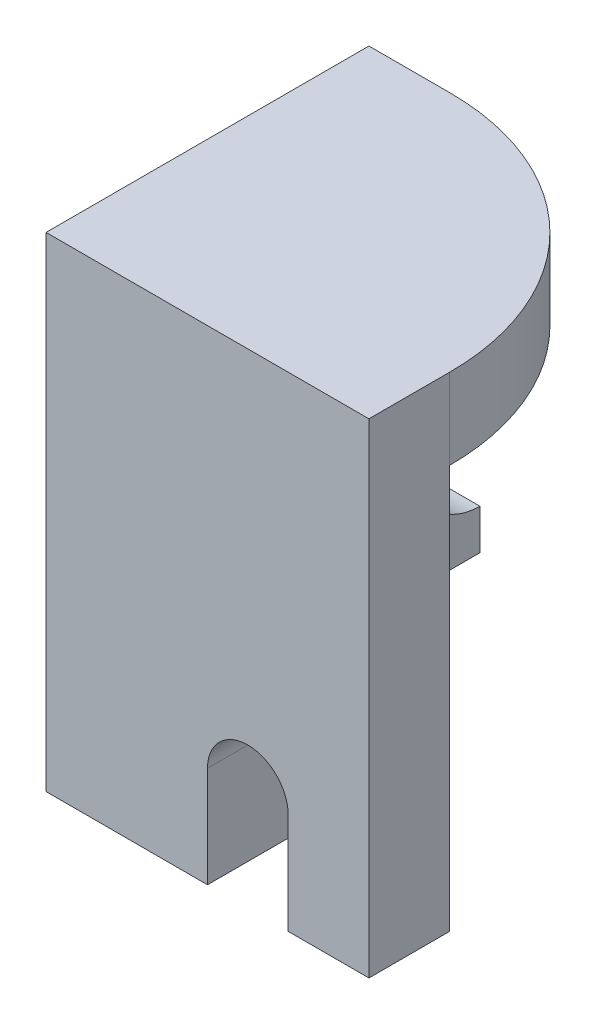
SolidWorks part; units mm, degrees
ref_plane "Front Plane" through (0, 0, 0) normal (0, 0, 1) x (1, 0, 0)
ref_plane "Top Plane" through (0, 0, 0) normal (0, 1, 0) x (1, 0, 0)
ref_plane "Right Plane" through (0, 0, 0) normal (1, 0, 0) x (0, 0, -1)
sketch "Sketch1" plane through (0, 0, 0) normal (0, 1, 0) x (1, 0, 0)
  line L0 (32, -32) -> (32, -16) construction
  line L1 (-32, 32) -> (-16, 32)
  line L2 (-32, 32) -> (-32, -32)
  line L3 (-32, -32) -> (32, -32)
  line L4 (32, -16) -> (32, -32)
  line L5 (-32, 32) -> (32, -32) construction
  line L6 (-32, -32) -> (32, 32) construction
  arc A0 (32, -16) -> (-16, 32) centre (-16, -16) ccw
  point P0 (0, 0)
  dimension "D3" = 48
  dimension "D1" = 64
  dimension "D2" = 64
extrude "Boss-Extrude1" add sketch "Sketch1" along normal blind 16
sketch "Sketch3" plane through (0, 0, 0) normal (0, -1, 0) x (1, 0, 0)
  line L0 (-32, -32) -> (-32, 32) construction
  line L1 (32, 32) -> (-32, 32)
  line L2 (32, 32) -> (32, 16)
  line L3 (32, 16) -> (-32, 16)
  line L4 (-32, 32) -> (-32, 16)
  dimension "D1" = 16
extrude "Boss-Extrude2" add sketch "Sketch3" along normal blind 80
sketch "Sketch4" plane through (0, 0, 16) normal (0, 0, -1) x (-1, 0, 0)
  line L0 (-32, -80) -> (-16, -80) construction
  line L1 (32, -80) -> (-32, -80) construction
  line L2 (-16, -80) -> (0, -80) construction
  line L4 (-16, -80) -> (0, -80)
  line L5 (-16, -80) -> (-16, -60)
  line L7 (0, -80) -> (0, -60)
  arc A0 (0, -60) -> (-16, -60) centre (-8, -60) ccw
  dimension "D1" = 20
extrude "Cut-Extrude1" cut sketch "Sketch4" against normal blind 80
sketch "Sketch5" plane through (0, 0, 16) normal (0, 0, -1) x (-1, 0, 0)
  line L1 (32, 0) -> (-10, 0)
  line L2 (32, 0) -> (32, -40)
  line L3 (32, -40) -> (-10, -40)
  line L4 (-10, 0) -> (-10, -40)
  dimension "D1" = 40
  dimension "D2" = 42
extrude "Boss-Extrude3" add sketch "Sketch5" along normal blind 28
sketch "Sketch6" plane through (10, 0, 0) normal (1, 0, 0) x (0, 0, -1)
  line L0 (12, 0) -> (12, -20) construction
  line L1 (12, 0) -> (12, -40) construction
  circle A0 centre (12, -20) radius 12
extrude "Cut-Extrude2" cut sketch "Sketch6" against normal blind 51
sketch "Sketch7" plane through (-32, 0, 0) normal (-1, 0, 0) x (0, 0, 1)
  line L0 (-12, -40) -> (16, -80)
  line L1 (16, -80) -> (16, -40)
  line L2 (-12, -40) -> (16, -40) construction
  line L3 (16, -80) -> (16, -40) construction
  line L4 (16, -40) -> (-12, -40)
extrude "Boss-Extrude4" add sketch "Sketch7" against normal blind 12
